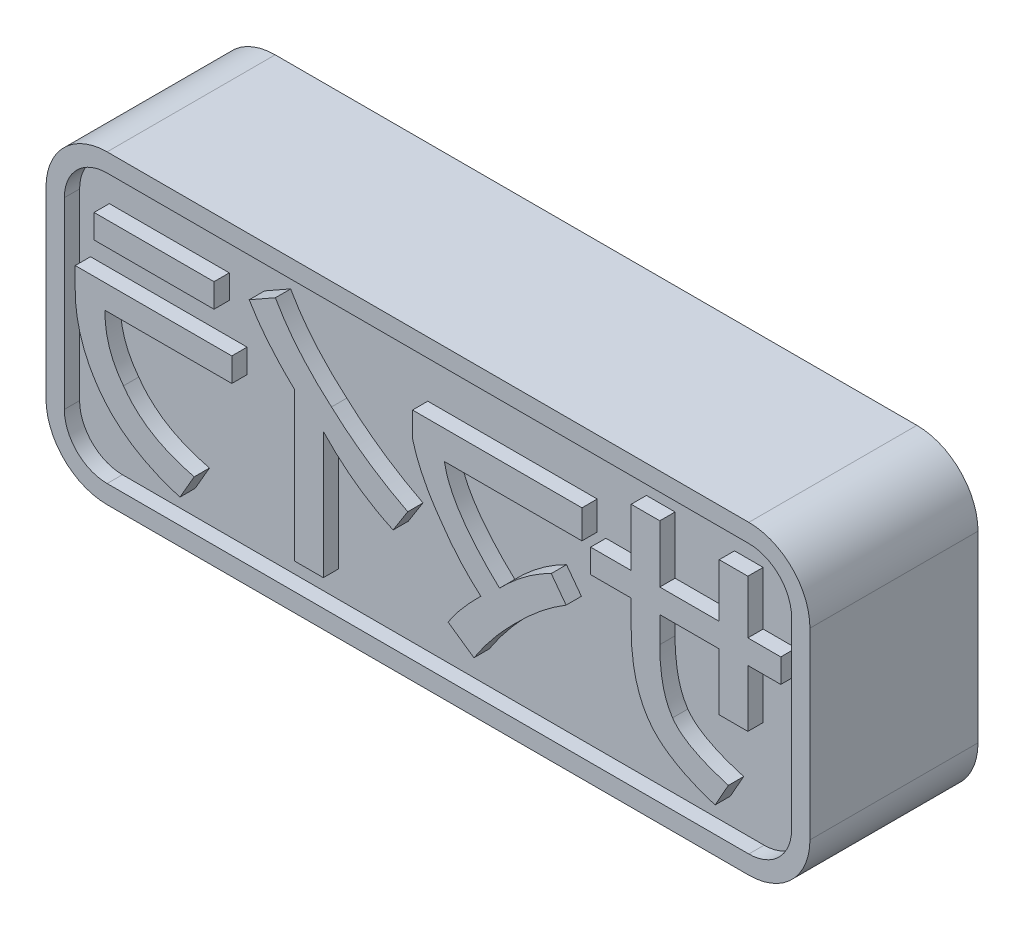
SolidWorks part; units mm, degrees
ref_plane "Front Plane" through (0, 0, 0) normal (0, 0, 1) x (1, 0, 0)
ref_plane "Top Plane" through (0, 0, 0) normal (0, 1, 0) x (1, 0, 0)
ref_plane "Right Plane" through (0, 0, 0) normal (1, 0, 0) x (0, 0, -1)
sketch "Sketch1" plane through (0, 0, 0) normal (0, 0, 1) x (1, 0, 0)
  line L0 (-12.5, -5) -> (12.5, 5) construction
  line L1 (-10.5, 5) -> (10.5, 5)
  line L2 (-12.5, 3) -> (-12.5, -3)
  line L3 (-10.5, -5) -> (10.5, -5)
  line L4 (12.5, 3) -> (12.5, -3)
  arc A0 (12.5, 3) -> (10.5, 5) centre (10.5, 3) ccw
  arc A1 (12.5, -3) -> (10.5, -5) centre (10.5, -3) cw
  arc A2 (-10.5, -5) -> (-12.5, -3) centre (-10.5, -3) cw
  arc A3 (-12.5, 3) -> (-10.5, 5) centre (-10.5, 3) cw
  point P4 (0, 0)
  point P11 (12.5, -5)
  point P17 (-12.5, 5)
  dimension "D3" = 2
  dimension "D1" = 25
  dimension "D2" = 10
extrude "Boss-Extrude1" add sketch "Sketch1" along normal blind 5
sketch "Sketch2" plane through (0, 0, 5) normal (0, 0, 1) x (1, 0, 0)
  line L0 (10.5, 4.4) -> (-10.5, 4.4)
  line L1 (-11.9, 3) -> (-11.9, -3)
  line L2 (-10.5, -4.4) -> (10.5, -4.4)
  line L3 (11.9, -3) -> (11.9, 3)
  line L4 (10.5, 5) -> (-10.5, 5)
  line L5 (-12.5, 3) -> (-12.5, -3)
  line L6 (-10.5, -5) -> (10.5, -5)
  line L7 (12.5, -3) -> (12.5, 3)
  line L8 (10.5, 5) -> (-10.5, 5)
  line L9 (-12.5, 3) -> (-12.5, -3)
  line L10 (-10.5, -5) -> (10.5, -5)
  line L11 (12.5, -3) -> (12.5, 3)
  arc A0 (-10.5, 4.4) -> (-11.9, 3) centre (-10.5, 3) ccw
  arc A1 (-11.9, -3) -> (-10.5, -4.4) centre (-10.5, -3) ccw
  arc A2 (10.5, -4.4) -> (11.9, -3) centre (10.5, -3) ccw
  arc A3 (11.9, 3) -> (10.5, 4.4) centre (10.5, 3) ccw
  arc A4 (12.5, 3) -> (10.5, 5) centre (10.5, 3) ccw
  arc A5 (-10.5, 5) -> (-12.5, 3) centre (-10.5, 3) ccw
  arc A6 (-12.5, -3) -> (-10.5, -5) centre (-10.5, -3) ccw
  arc A7 (10.5, -5) -> (12.5, -3) centre (10.5, -3) ccw
  arc A8 (12.5, 3) -> (10.5, 5) centre (10.5, 3) ccw
  arc A9 (-10.5, 5) -> (-12.5, 3) centre (-10.5, 3) ccw
  arc A10 (-12.5, -3) -> (-10.5, -5) centre (-10.5, -3) ccw
  arc A11 (10.5, -5) -> (12.5, -3) centre (10.5, -3) ccw
  dimension "D1" = 0
  dimension "D2" = 0.6
extrude "Boss-Extrude2" add sketch "Sketch2" along normal blind 0.5
sketch "Sketch3" plane through (0, 0, 5) normal (0, 0, 1) x (1, 0, 0)
  text T0 "サマイラ\r\n\r\n" font "MS UI Gothic" height in points 19
extrude "Boss-Extrude3" add sketch "Sketch3" along normal blind 0.5
sketch "Sketch4" plane through (0, 0, 0) normal (0, 0, -1) x (-1, 0, 0)
  line L0 (2, 2) -> (-2, -2) construction
  line L1 (-2, 2) -> (2, 2)
  line L2 (-2, 2) -> (-2, -2)
  line L3 (-2, -2) -> (2, -2)
  line L4 (2, 2) -> (2, -2)
  point P4 (0, 0)
  point P6 (3.4688, -2.0911)
  point P7 (3.5653, -2.0911)
  dimension "D1" = 4
  dimension "D2" = 4
extrude "Cut-Extrude1" cut sketch "Sketch4" against normal blind 4
